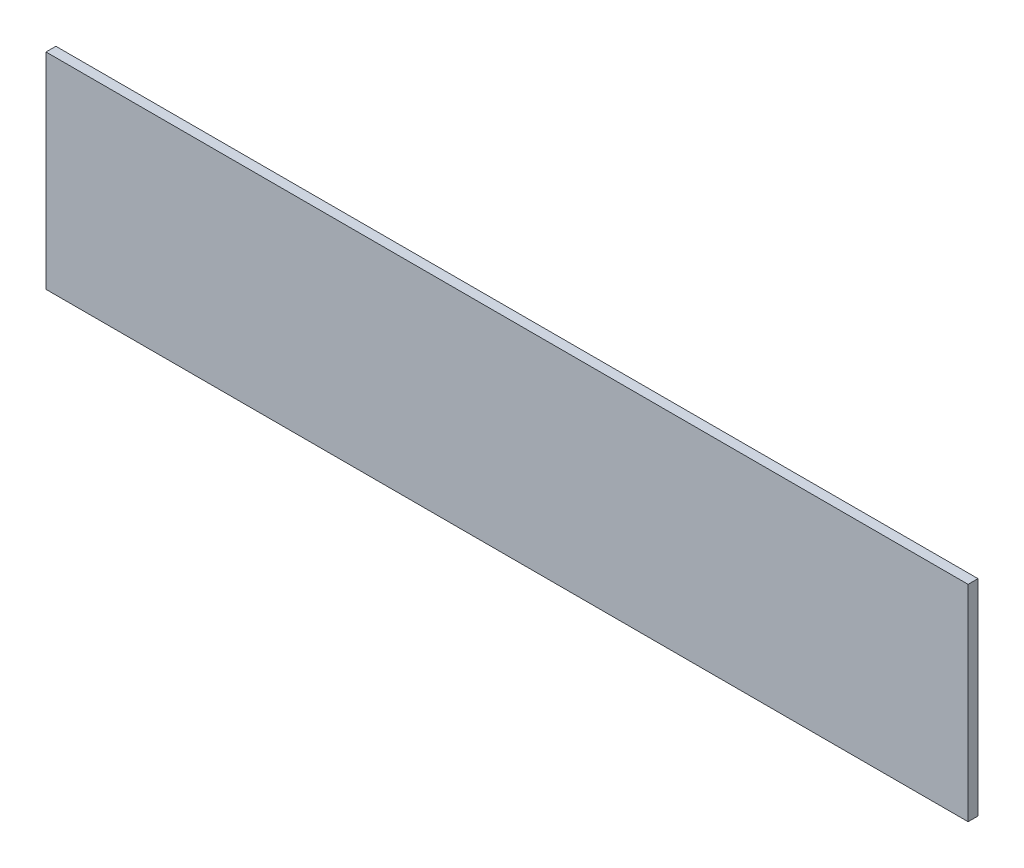
SolidWorks part; units mm, degrees
ref_plane "Front Plane" through (0, 0, 0) normal (0, 0, 1) x (1, 0, 0)
ref_plane "Top Plane" through (0, 0, 0) normal (0, 1, 0) x (1, 0, 0)
ref_plane "Right Plane" through (0, 0, 0) normal (1, 0, 0) x (0, 0, -1)
sketch "Sketch1" plane through (0, 0, 0) normal (0, 0, 1) x (1, 0, 0)
  line L1 (0, 0) -> (592, 0)
  line L2 (0, 0) -> (0, 132)
  line L3 (0, 132) -> (592, 132)
  line L4 (592, 0) -> (592, 132)
  dimension "D1" = 132
  dimension "D2" = 592
extrude "Boss-Extrude1" add sketch "Sketch1" along normal blind 6.35
